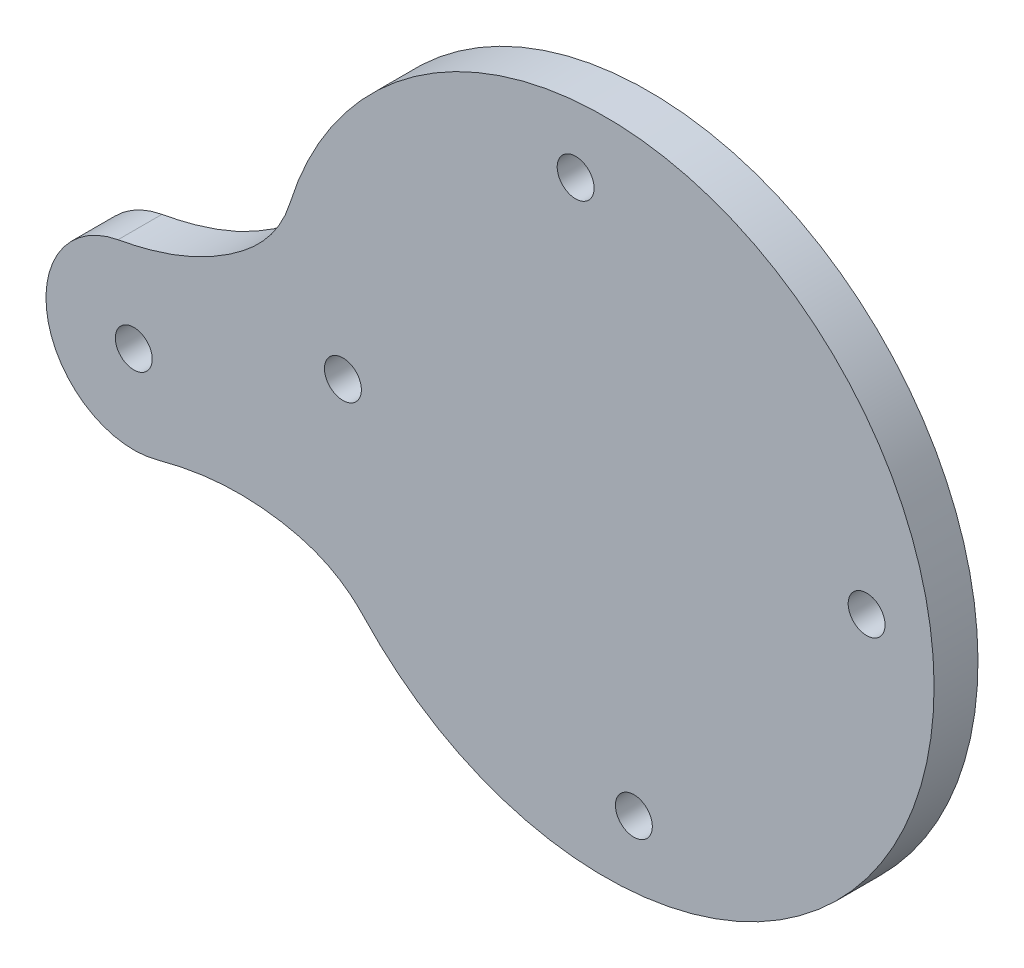
SolidWorks part; units mm, degrees
ref_plane "Plan de face" through (0, 0, 0) normal (0, 0, 1) x (1, 0, 0)
ref_plane "Plan de dessus" through (0, 0, 0) normal (0, 1, 0) x (1, 0, 0)
ref_plane "Plan de droite" through (0, 0, 0) normal (1, 0, 0) x (0, 0, -1)
sketch "Esquisse1" plane through (0, 0, 0) normal (0, 0, 1) x (1, 0, 0)
  circle A0 centre (0, 0) radius 37.5
extrude "Boss.-Extru.1" add sketch "Esquisse1" along normal blind 5
hole_wizard "Trou pour taraudage pour trou taraudé M51" positions "Esquisse2" profile "Esquisse3" hole size "M5" standard "ISO" end condition through all
sketch "Esquisse2" plane through (0, 0, 5) normal (0, 0, 1) x (1, 0, 0)
  circle A0 centre (0, 0) radius 30
  point P0 (3.3163, -29.8161)
sketch "Esquisse3" plane through (3.3163, -29.8161, 5) normal (1, 0, 0) x (0, -1, 0)
  line L0 (0, 0) -> (0, 5)
  line L1 (0, 5) -> (2.1, 5)
  line L2 (2.1, 5) -> (2.1, 0)
  line L5 (2.1, 0) -> (0, 0)
  line L11 (0, -6.35) -> (0, 107.95) construction
  dimension "Diamètre du perçage jusqu'au prochain" = 4.2
  dimension "Profondeur du perçage jusqu'au prochain" = 5
pattern_circular "Répétition circulaire1" count 4 over 360 about axis through (0, 0, 0) along (0, 0, 1) of "Trou pour taraudage pour trou taraudé M51"
sketch "Esquisse4" plane through (0, 0, 5) normal (0, 0, 1) x (1, 0, 0)
  line L0 (0, 0) -> (-53.6282, -12.207) construction
  arc A0 (-55.4277, -2.3702) -> (-50.9929, -21.8535) centre (-53.6282, -12.207) ccw
  circle A1 centre (0, 0) radius 37.5 construction
  circle A3 centre (0, 0) radius 37.5
  arc A4 (-35.8163, 11.1104) -> (-27.4789, -25.5178) centre (0, 0) ccw
  spline S0 degree 3 poles (-27.4789, -25.5178) (-30.3182, -22.4604) (-38.3337, -19.8574) (-46.1741, -20.537) (-50.9929, -21.8535) knots 0 0 0 0 0.45021 1 1 1 1
  spline S1 degree 3 poles (-35.8163, 11.1104) (-37.0525, 7.1253) (-43.1517, 1.3095) (-50.5139, -1.4713) (-55.4277, -2.3702) knots 0 0 0 0 0.45021 1 1 1 1
  dimension "D1" = 20
  dimension "D2" = 55
  dimension "D3" = 0
extrude "Boss.-Extru.2" add sketch "Esquisse4" against normal blind 5
hole_wizard "Trou pour taraudage pour trou taraudé M52" positions "Esquisse6" profile "Esquisse7" hole size "M5" standard "ISO" end condition through all
sketch "Esquisse6" plane through (0, 0, 5) normal (0, 0, 1) x (1, 0, 0)
  point P0 (-53.6282, -12.207)
sketch "Esquisse7" plane through (-53.6282, -12.207, 5) normal (1, 0, 0) x (0, -1, 0)
  line L0 (0, 0) -> (0, 5)
  line L1 (0, 5) -> (2.1, 5)
  line L2 (2.1, 5) -> (2.1, 0)
  line L5 (2.1, 0) -> (0, 0)
  line L11 (0, -6.35) -> (0, 107.95) construction
  dimension "Diamètre du perçage jusqu'au prochain" = 4.2
  dimension "Profondeur du perçage jusqu'au prochain" = 5
